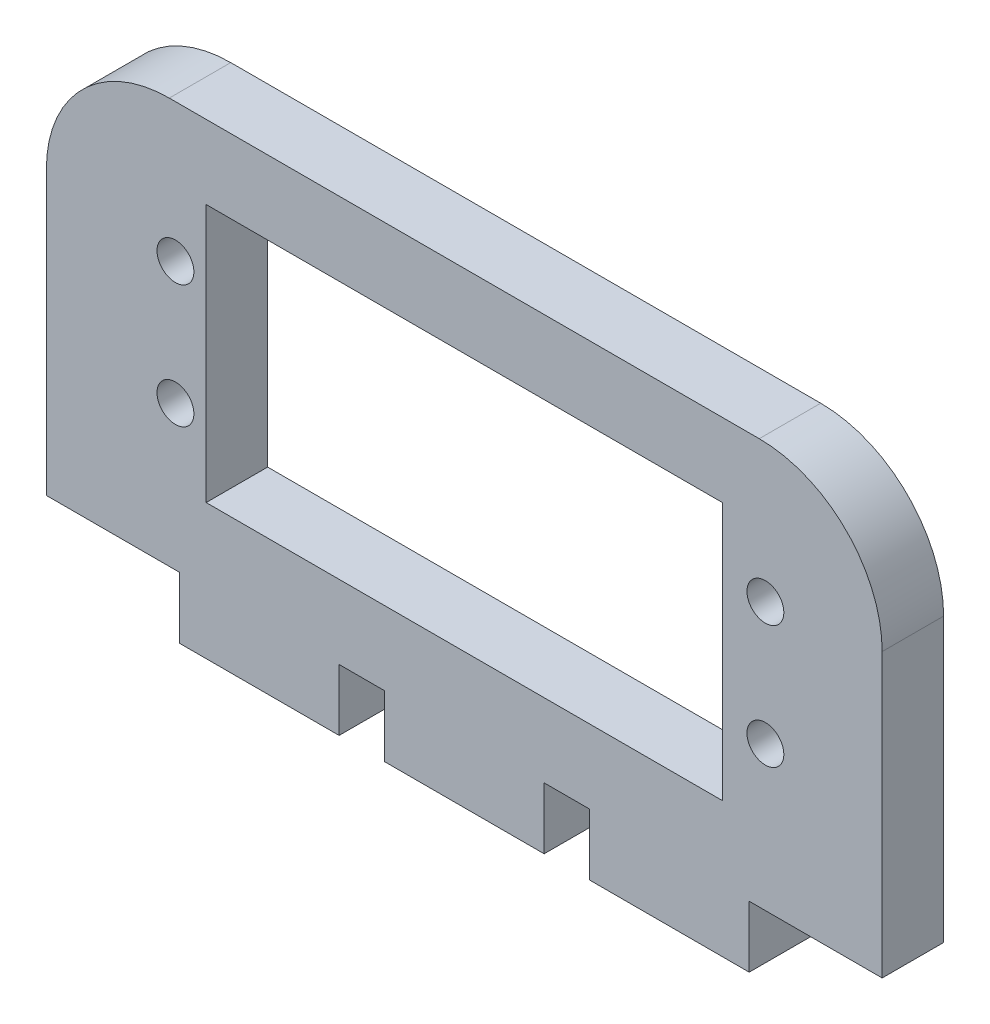
SolidWorks part; units mm, degrees
material "Acrylic (Medium-high impact)"
ref_plane "Front Plane" through (0, 0, 0) normal (0, 0, 1) x (1, 0, 0)
ref_plane "Top Plane" through (0, 0, 0) normal (0, 1, 0) x (1, 0, 0)
ref_plane "Right Plane" through (0, 0, 0) normal (1, 0, 0) x (0, 0, -1)
sketch "Sketch1" plane through (0, 0, 0) normal (0, 0, 1) x (1, 0, 0)
  line L0 (-28.087, 0) -> (-17.2691, 0)
  line L1 (39.913, 0) -> (39.913, 33)
  line L2 (39.913, 33) -> (-28.087, 33)
  line L3 (-28.087, 33) -> (-28.087, 0)
  line L5 (-17.2691, -5) -> (-4.2691, -5)
  line L6 (29.0952, 0) -> (29.0952, -5)
  line L7 (-17.2691, 0) -> (-17.2691, -5)
  line L8 (-4.2691, -5) -> (-4.2691, 0)
  line L9 (16.0952, -5) -> (16.0952, 0)
  line L10 (-0.587, -5) -> (-0.587, 0)
  line L11 (12.413, -5) -> (12.413, 0)
  line L12 (-0.587, -5) -> (12.413, -5)
  line L14 (16.0952, -5) -> (29.0952, -5)
  line L16 (5.913, -5) -> (5.913, 33) construction
  line L17 (12.413, 0) -> (16.0952, 0)
  line L18 (29.0952, 0) -> (39.913, 0)
  line L19 (-4.2691, 0) -> (-0.587, 0)
  line L20 (-15.087, 6) -> (26.913, 6)
  line L21 (-15.087, 27) -> (26.913, 27)
  line L22 (26.913, 27) -> (26.913, 6)
  line L23 (-15.087, 6) -> (-15.087, 27)
  circle A0 centre (30.413, 21.75) radius 1.5
  circle A1 centre (30.413, 11.75) radius 1.5
  circle A2 centre (-17.587, 21.75) radius 1.5
  circle A3 centre (-17.587, 11.75) radius 1.5
  dimension "D6" = 3
  dimension "D7" = 3
  dimension "D8" = 3
  dimension "D9" = 3
  dimension "D1" = 68
  dimension "D2" = 21
  dimension "D3" = 6
  dimension "D4" = 6
  dimension "D5" = 21
extrude "Boss-Extrude1" add sketch "Sketch1" along normal blind 5
fillet "Fillet2" radius 10 1 edges at (-28.087, 33, 2.5)
fillet "Fillet3" radius 10 1 edges at (39.913, 33, 2.5)
